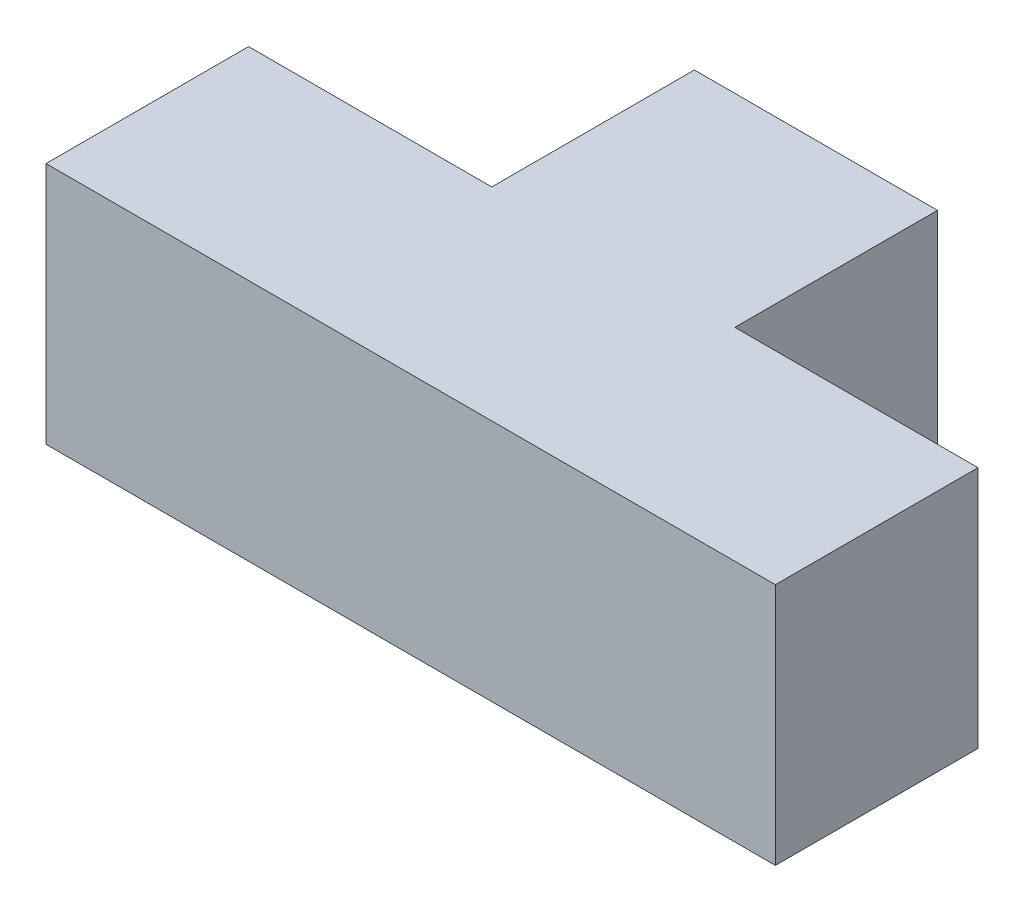
SolidWorks part; units mm, degrees
ref_plane "Front Plane" through (0, 0, 0) normal (0, 0, 1) x (1, 0, 0)
ref_plane "Top Plane" through (0, 0, 0) normal (0, 1, 0) x (1, 0, 0)
ref_plane "Right Plane" through (0, 0, 0) normal (1, 0, 0) x (0, 0, -1)
sketch "Sketch1" plane through (0, 0, 0) normal (0, 1, 0) x (1, 0, 0)
  line L0 (0, 0) -> (-90, 0)
  line L1 (0, 0) -> (0, 25)
  line L2 (0, 25) -> (-30, 25)
  line L3 (-30, 25) -> (-30, 50)
  line L4 (-30, 50) -> (-60, 50)
  line L5 (-45, 50) -> (-45, -32.3683) construction
  line L6 (-90, 0) -> (-90, 25)
  line L7 (-90, 25) -> (-60, 25)
  line L8 (-60, 25) -> (-60, 50)
  point P10 (-45, 0)
  dimension "D1" = 90
  dimension "D2" = 25
  dimension "D3" = 25
  dimension "D4" = 30
extrude "Boss-Extrude1" add sketch "Sketch1" along normal blind 30
